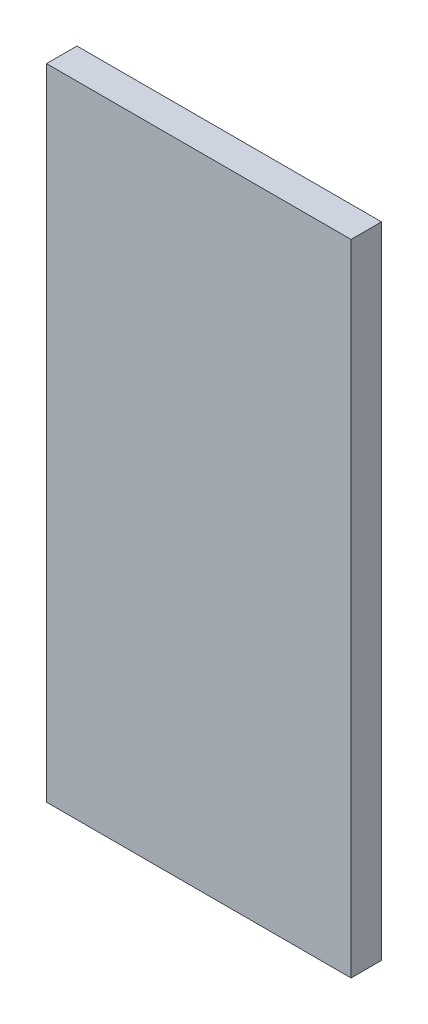
SolidWorks part; units mm, degrees
ref_plane "Alzado" through (0, 0, 0) normal (0, 0, 1) x (1, 0, 0)
ref_plane "Planta" through (0, 0, 0) normal (0, 1, 0) x (1, 0, 0)
ref_plane "Vista lateral" through (0, 0, 0) normal (1, 0, 0) x (0, 0, -1)
sketch "Croquis1" plane through (0, 0, 0) normal (0, 0, 1) x (1, 0, 0)
  line L1 (0, 0) -> (1000, 0)
  line L2 (0, 0) -> (0, -2100)
  line L3 (0, -2100) -> (1000, -2100)
  line L4 (1000, 0) -> (1000, -2100)
  dimension "D1" = 1000
  dimension "D2" = 2100
extrude "Saliente-Extruir1" add sketch "Croquis1" along normal blind 100
